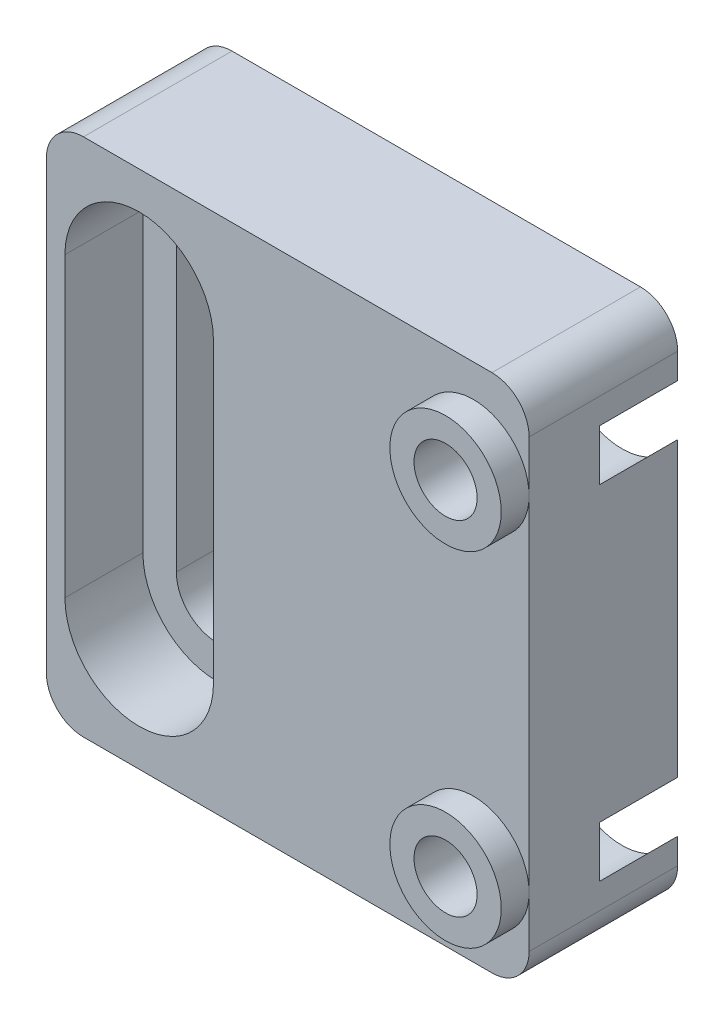
SolidWorks part; units mm, degrees
ref_plane "Plan de face" through (0, 0, 0) normal (0, 0, 1) x (1, 0, 0)
ref_plane "Plan de dessus" through (0, 0, 0) normal (0, 1, 0) x (1, 0, 0)
ref_plane "Plan de droite" through (0, 0, 0) normal (1, 0, 0) x (0, 0, -1)
sketch "Esquisse1" plane through (0, 0, 0) normal (0, 0, 1) x (1, 0, 0)
  line L1 (-8, 14) -> (18, 14)
  line L2 (-8, 14) -> (-8, -14)
  line L3 (-8, -14) -> (18, -14)
  line L4 (18, 14) -> (18, -14)
  dimension "D1" = 28
  dimension "D2" = 26
  dimension "D3" = 14
  dimension "D4" = 8
extrude "Boss.-Extru.1" add sketch "Esquisse1" along normal blind 8
sketch "Esquisse2" plane through (0, 0, 8) normal (0, 0, 1) x (1, 0, 0)
  line L2 (-3, 8) -> (-3, -8) construction
  line L3 (-0.8, 8) -> (-0.8, -8)
  line L4 (-5.2, 8) -> (-5.2, -8)
  line L5 (-8, -14) -> (18, -14) construction
  line L6 (-8, 14) -> (-8, -14) construction
  arc A1 (-0.8, 8) -> (-5.2, 8) centre (-3, 8) ccw
  arc A2 (-5.2, -8) -> (-0.8, -8) centre (-3, -8) ccw
  point P8 (-3, 0)
  dimension "D1" = 2.8
  dimension "D4" = 2.2
  dimension "D5" = 16
  dimension "D6" = 6
extrude "Enlèv. mat.-Extru.1" cut sketch "Esquisse2" against normal through all
sketch "Esquisse3" plane through (0, 0, 8) normal (0, 0, 1) x (1, 0, 0)
  line L0 (-3, 8) -> (-3, -8) construction
  line L1 (1, 8) -> (1, -8)
  line L2 (-7, 8) -> (-7, -8)
  line L3 (18, 14) -> (-8, 14) construction
  line L4 (-8, -14) -> (18, -14) construction
  line L5 (-8, 14) -> (-8, -14) construction
  arc A2 (1, 8) -> (-7, 8) centre (-3, 8) ccw
  arc A3 (-7, -8) -> (1, -8) centre (-3, -8) ccw
  point P6 (-3, 0)
  dimension "D1" = 1
  dimension "D2" = 4
  dimension "D3" = 6
  dimension "D4" = 6
extrude "Enlèv. mat.-Extru.2" cut sketch "Esquisse3" against normal blind 4.2
sketch "Esquisse4" plane through (0, 0, 8) normal (0, 0, 1) x (1, 0, 0)
  line L0 (18, -14) -> (18, 14) construction
  circle A0 centre (15, 9.25) radius 1.7
  circle A1 centre (15, -9.25) radius 1.7
  dimension "D2" = 3.4
  dimension "D3" = 3.4
  dimension "D1" = 18.5
  dimension "D4" = 3
  dimension "D5" = 3
  dimension "D6" = 9.25
extrude "Enlèv. mat.-Extru.3" cut sketch "Esquisse4" against normal through all
sketch "Esquisse5" plane through (0, 0, 0) normal (0, 0, -1) x (-1, 0, 0)
  circle A0 centre (-15, 9.25) radius 3.3
  circle A1 centre (-15, -9.25) radius 3.3
  dimension "D1" = 6.6
  dimension "D2" = 6.6
extrude "Enlèv. mat.-Extru.6" cut sketch "Esquisse5" against normal blind 4.2
sketch "Esquisse6" plane through (0, 0, 4.2) normal (0, 0, -1) x (-1, 0, 0)
  circle A0 centre (-15, 9.25) radius 1.7
  circle A1 centre (-15, -9.25) radius 1.7
extrude "Boss.-Extru.2" add sketch "Esquisse6" against normal blind 1
sketch "Esquisse7" plane through (0, 0, 8) normal (0, 0, 1) x (1, 0, 0)
  circle A0 centre (15, 9.25) radius 1.7
  circle A1 centre (15, -9.25) radius 1.7
  circle A2 centre (15, -9.25) radius 3
  circle A3 centre (15, 9.25) radius 3
extrude "Boss.-Extru.3" add sketch "Esquisse7" along normal blind 1.5
fillet "Fillet1" radius 2 4 edges at (-8, -14, 4) (-8, 14, 4) (18, -14, 4) (18, 14, 4)
